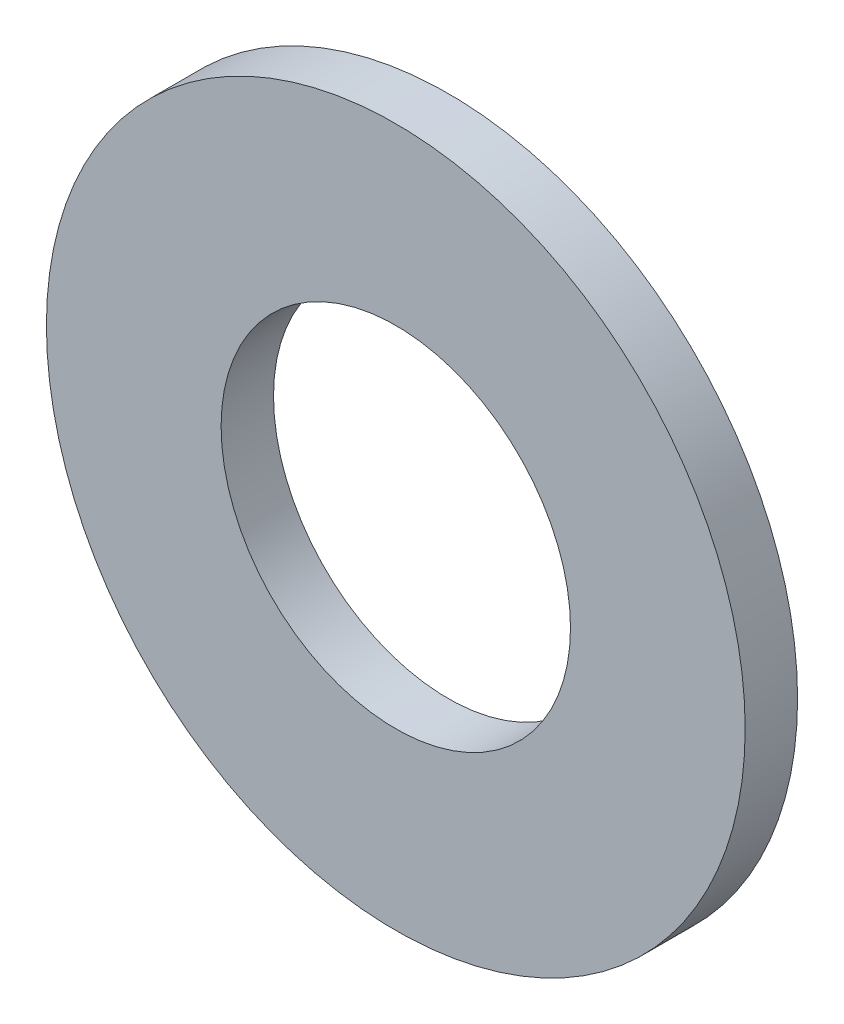
SolidWorks part; units mm, degrees
ref_plane "Front Plane" through (0, 0, 0) normal (0, 0, 1) x (1, 0, 0)
ref_plane "Top Plane" through (0, 0, 0) normal (0, 1, 0) x (1, 0, 0)
ref_plane "Right Plane" through (0, 0, 0) normal (1, 0, 0) x (0, 0, -1)
sketch "Sketch1" plane through (0, 0, 0) normal (0, 0, 1) x (1, 0, 0)
  circle A0 centre (0, 0) radius 4
  circle A1 centre (0, 0) radius 2
  dimension "D1" = 8
  dimension "D2" = 4
extrude "Boss-Extrude1" add sketch "Sketch1" along normal blind 0.6
